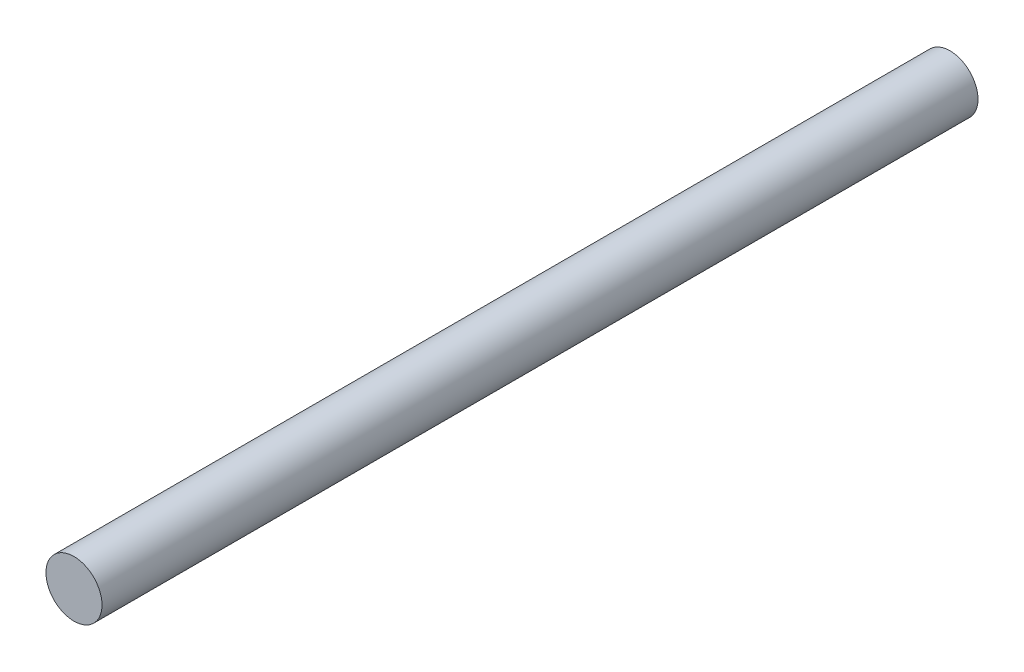
SolidWorks part; units mm, degrees
ref_plane "Ön Düzlem" through (0, 0, 0) normal (0, 0, 1) x (1, 0, 0)
ref_plane "Üst Düzlem" through (0, 0, 0) normal (0, 1, 0) x (1, 0, 0)
ref_plane "Sağ Düzlem" through (0, 0, 0) normal (1, 0, 0) x (0, 0, -1)
sketch "Çizim1" plane through (0, 0, 0) normal (0, 0, 1) x (1, 0, 0)
  circle A0 centre (0, 0) radius 8
extrude "Yükseklik-Ekstrüzyon1" add sketch "Çizim1" along normal blind 250
